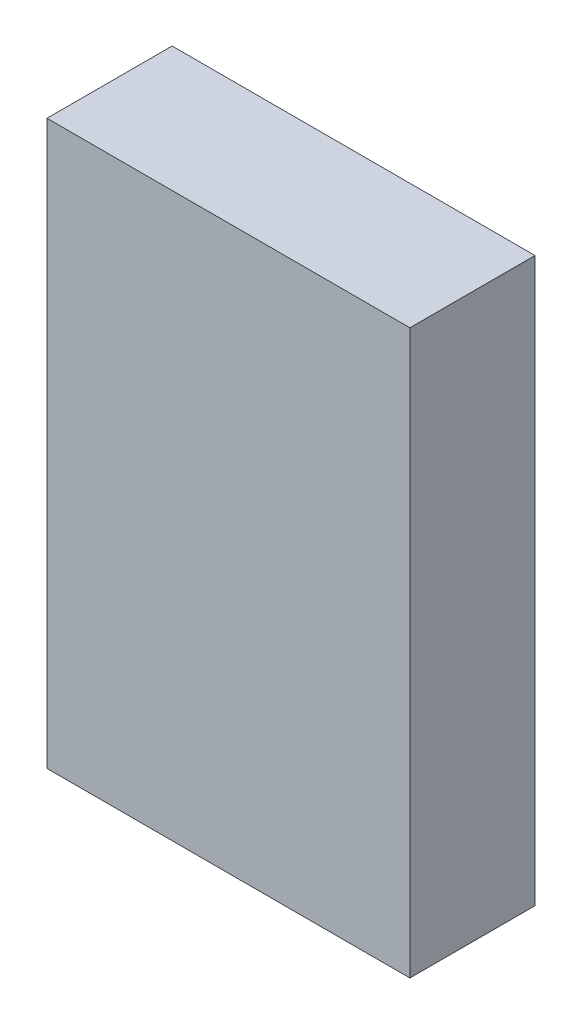
SolidWorks part; units mm, degrees
ref_plane "正面" through (0, 0, 0) normal (0, 0, 1) x (1, 0, 0)
ref_plane "平面" through (0, 0, 0) normal (0, 1, 0) x (1, 0, 0)
ref_plane "右側面" through (0, 0, 0) normal (1, 0, 0) x (0, 0, -1)
sketch "Sketch1" plane through (0, 0, 0) normal (0, 0, 1) x (1, 0, 0)
  line L1 (29, -45) -> (-29, -45)
  line L2 (29, -45) -> (29, 45)
  line L3 (29, 45) -> (-29, 45)
  line L4 (-29, -45) -> (-29, 45)
  line L5 (0, 45) -> (0, -45) construction
  line L6 (29, 0) -> (-29, 0) construction
  point P0 (0, 0)
  dimension "D1" = 90
  dimension "D2" = 58
extrude "Boss-Extrude1" add sketch "Sketch1" along normal blind 20
